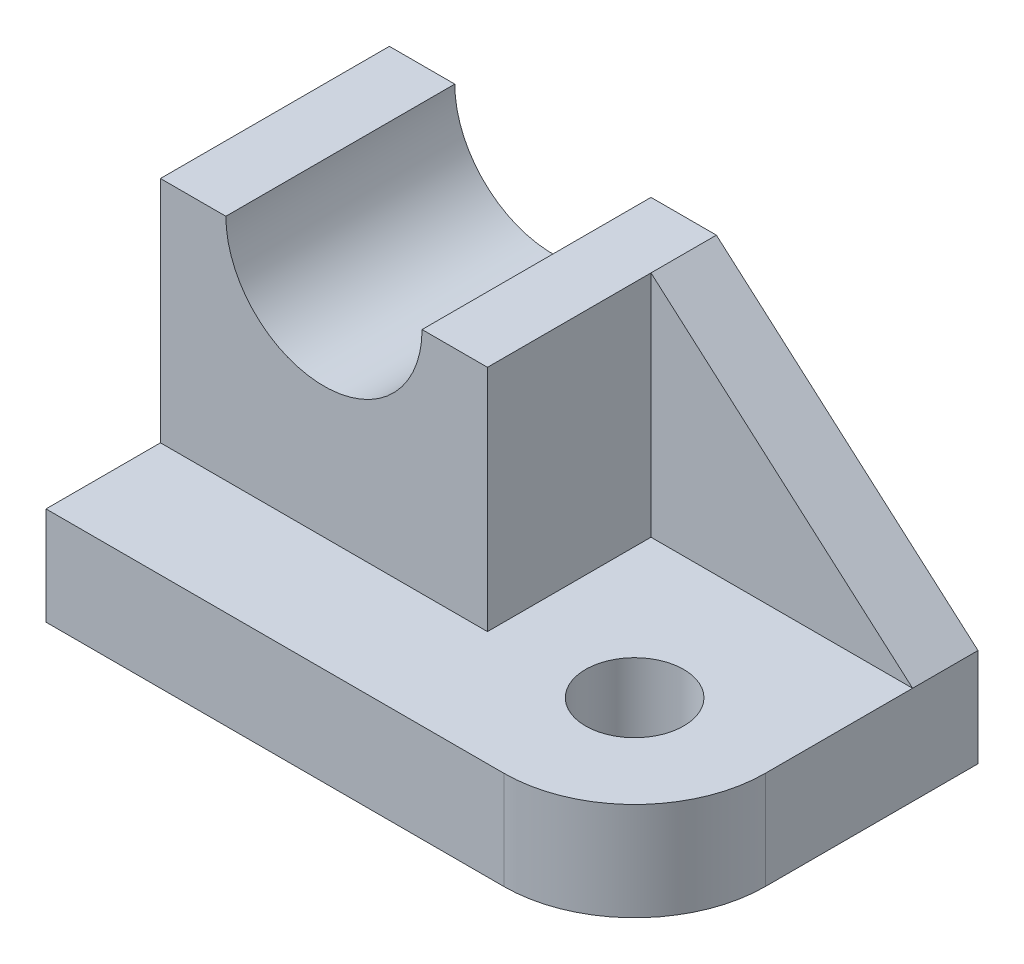
SolidWorks part; units mm, degrees
ref_plane "Front Plane" through (0, 0, 0) normal (0, 0, 1) x (1, 0, 0)
ref_plane "Top Plane" through (0, 0, 0) normal (0, 1, 0) x (1, 0, 0)
ref_plane "Right Plane" through (0, 0, 0) normal (1, 0, 0) x (0, 0, -1)
sketch "Sketch1" plane through (0, 0, 0) normal (0, 1, 0) x (1, 0, 0)
  line L5 (-36, 21) -> (36, 21)
  line L6 (-36, 21) -> (-36, -21)
  line L7 (-36, -21) -> (36, -21)
  line L8 (36, 21) -> (36, -21)
  point P8 (3.5781, -2.167)
  point P9 (-1.2232, -0.3503)
  dimension "D1" = 36
  dimension "D2" = 21
  dimension "D3" = 42
  dimension "D4" = 72
extrude "Boss-Extrude1" add sketch "Sketch1" along normal blind 12
sketch "Sketch2" plane through (0, 12, 0) normal (0, 1, 0) x (1, 0, 0)
  line L1 (-36, 21) -> (4, 21)
  line L2 (-36, 21) -> (-36, -7)
  line L3 (-36, -7) -> (4, -7)
  line L4 (4, 21) -> (4, -7)
  dimension "D1" = 28
  dimension "D2" = 40
extrude "Boss-Extrude2" add sketch "Sketch2" along normal blind 28
sketch "Sketch3" plane through (0, 0, 7) normal (0, 0, 1) x (1, 0, 0)
  line L0 (-36, 40) -> (4, 40) construction
  circle A0 centre (-16, 40) radius 12
  dimension "D1" = 24
extrude "Cut-Extrude1" cut sketch "Sketch3" against normal through all
sketch "Sketch4" plane through (0, 0, -21) normal (0, 0, -1) x (-1, 0, 0)
  line L0 (-4, 40) -> (-4, 12)
  line L1 (-4, 12) -> (-36, 12)
  line L2 (-36, 12) -> (-4, 40)
extrude "Boss-Extrude3" add sketch "Sketch4" against normal blind 8
fillet "Fillet3" radius 16 1 edges at (36, 6, 21)
sketch "Sketch5" plane through (0, 12, 0) normal (0, 1, 0) x (1, 0, 0)
  circle A0 centre (20, -5) radius 6
  dimension "D3" = 12
  dimension "D1" = 16
  dimension "D2" = 16
extrude "Cut-Extrude2" cut sketch "Sketch5" against normal through all
